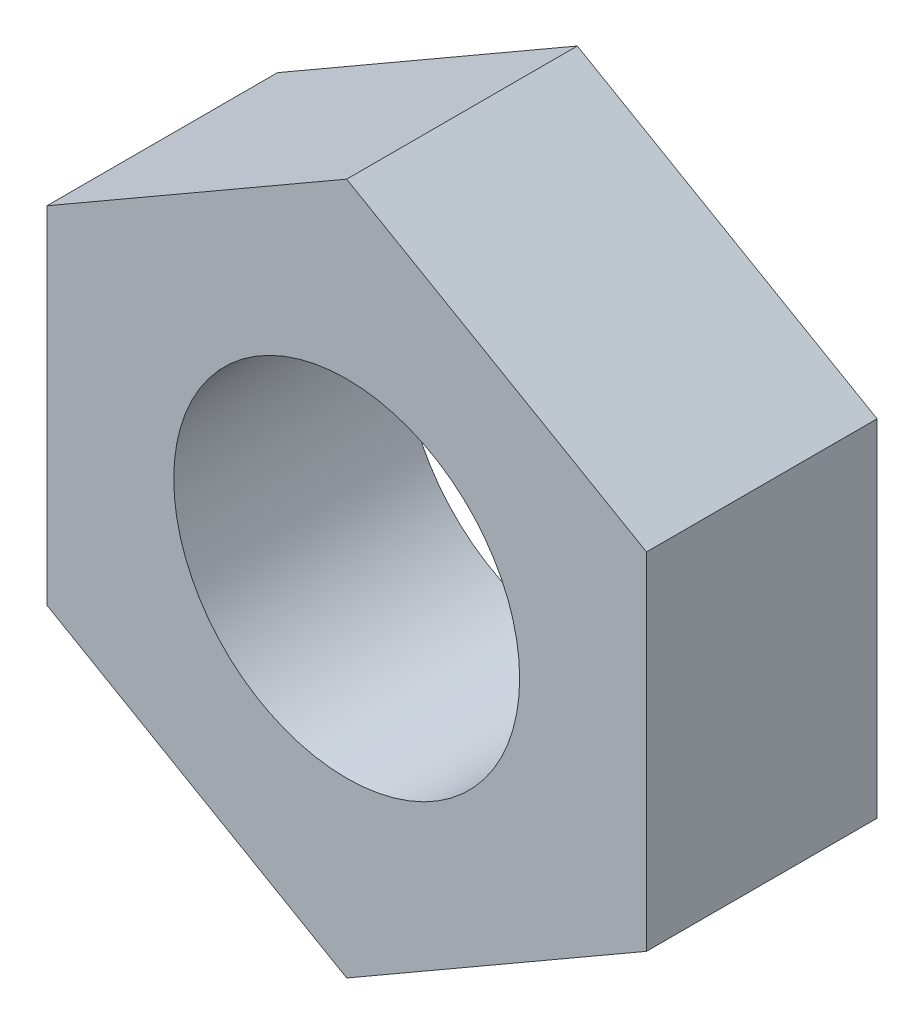
SolidWorks part; units mm, degrees
ref_plane "Alzado" through (0, 0, 0) normal (0, 0, 1) x (1, 0, 0)
ref_plane "Planta" through (0, 0, 0) normal (0, 1, 0) x (1, 0, 0)
ref_plane "Vista lateral" through (0, 0, 0) normal (1, 0, 0) x (0, 0, -1)
sketch "Croquis1" plane through (0, 0, 0) normal (0, 0, 1) x (1, 0, 0)
  line L0 (0, 0) -> (0, 12) construction
  line L1 (0, 6) -> (-5.2, 6) construction
  line L2 (0, 6) -> (5.2, 6) construction
  line L3 (5.2, 3) -> (5.2, 9)
  line L4 (-5.2, 3) -> (-5.2, 9)
  line L5 (-5.2, 9) -> (0, 12)
  line L6 (0, 12) -> (5.2, 9)
  line L7 (5.2, 3) -> (0, 0)
  line L8 (0, 0) -> (-5.2, 3)
  circle A1 centre (0, 6) radius 3
  point P6 (5.2, 0)
  point P10 (5.2, 6)
  point P13 (-5.2, 6)
  dimension "D1" = 12
  dimension "D2" = 5.2
  dimension "D3" = 5.2
  dimension "D4" = 6
  dimension "D5" = 6
extrude "Saliente-Extruir1" add sketch "Croquis1" along normal blind 4
